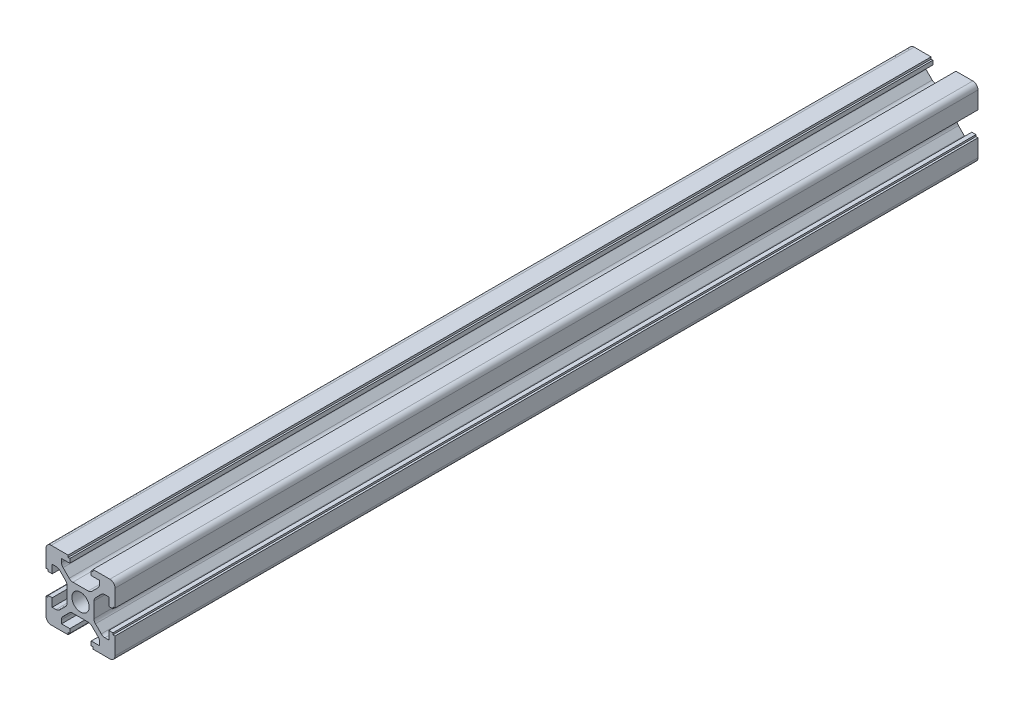
SolidWorks part; units mm, degrees
ref_plane "Front Plane" through (0, 0, 0) normal (0, 0, 1) x (1, 0, 0)
ref_plane "Top Plane" through (0, 0, 0) normal (0, 1, 0) x (1, 0, 0)
ref_plane "Right Plane" through (0, 0, 0) normal (1, 0, 0) x (0, 0, -1)
sketch "Sketch1" plane through (0, 0, 0) normal (0, 0, 1) x (1, 0, 0)
  line L0 (-3.6, -10) -> (-8.5, -10)
  line L1 (-10, -8.5) -> (-10, -3.5)
  line L2 (0, 0) -> (-10, -10) construction
  line L3 (0, 0) -> (0, 11.6126) construction
  line L4 (0, 0) -> (11.7731, -11.7731) construction
  line L5 (8.5, -10) -> (3.6, -10)
  line L6 (10, -8.5) -> (10, -3.5)
  line L7 (3.6, -10) -> (3.6, -9.4)
  line L8 (3.6, -9.4) -> (3.1, -9.4)
  line L9 (3.1, -9.4) -> (3.1, -8.2)
  line L10 (-3.6, -10) -> (-3.6, -9.4)
  line L11 (-3.6, -9.4) -> (-3.1, -9.4)
  line L12 (-3.1, -9.4) -> (-3.1, -8.2)
  line L13 (3.1, -8.2) -> (5.5, -8.2)
  line L14 (-3.1, -8.2) -> (-5.5, -8.2)
  line L15 (-5.5, -8.2) -> (-5.5, -7.182)
  line L16 (-5.0607, -6.1213) -> (-3.2787, -4.3393)
  line L17 (5.5, -8.2) -> (5.5, -7.182)
  line L18 (5.0607, -6.1213) -> (3.2787, -4.3393)
  line L19 (-2.218, -3.9) -> (2.218, -3.9)
  line L20 (-10, -3.5) -> (-9.4, -3.5)
  line L21 (-9.4, -3.5) -> (-9.4, -3)
  line L22 (-9.4, -3) -> (-8.2, -3)
  line L23 (-8.2, -3) -> (-8.2, -5.4)
  line L24 (-8.2, -5.4) -> (-7.082, -5.4)
  line L25 (-6.0213, -4.9607) -> (-4.3393, -3.2787)
  line L26 (-3.9, -2.218) -> (-3.9, 2.218)
  line L27 (10, -3.5) -> (9.4, -3.5)
  line L28 (9.4, -3.5) -> (9.4, -3)
  line L29 (9.4, -3) -> (8.2, -3)
  line L30 (8.2, -3) -> (8.2, -5.4)
  line L31 (8.2, -5.4) -> (7.082, -5.4)
  line L32 (6.0213, -4.9607) -> (4.3393, -3.2787)
  line L33 (3.9, -2.218) -> (3.9, 2.218)
  line L34 (0, 0) -> (-21.3742, 0) construction
  line L35 (6.0213, 4.9607) -> (4.3393, 3.2787)
  line L36 (8.2, 5.4) -> (7.082, 5.4)
  line L37 (8.2, 3) -> (8.2, 5.4)
  line L38 (9.4, 3) -> (8.2, 3)
  line L39 (9.4, 3.5) -> (9.4, 3)
  line L40 (10, 3.5) -> (9.4, 3.5)
  line L41 (10, 8.5) -> (10, 3.5)
  line L42 (8.5, 10) -> (3.6, 10)
  line L43 (3.6, 10) -> (3.6, 9.4)
  line L44 (3.6, 9.4) -> (3.1, 9.4)
  line L45 (3.1, 9.4) -> (3.1, 8.2)
  line L46 (3.1, 8.2) -> (5.5, 8.2)
  line L47 (5.5, 8.2) -> (5.5, 7.182)
  line L48 (5.0607, 6.1213) -> (3.2787, 4.3393)
  line L49 (-2.218, 3.9) -> (2.218, 3.9)
  line L50 (-5.0607, 6.1213) -> (-3.2787, 4.3393)
  line L51 (-5.5, 8.2) -> (-5.5, 7.182)
  line L52 (-3.1, 8.2) -> (-5.5, 8.2)
  line L53 (-3.6, 9.4) -> (-3.1, 9.4)
  line L54 (-3.1, 9.4) -> (-3.1, 8.2)
  line L55 (-3.6, 10) -> (-3.6, 9.4)
  line L56 (-3.6, 10) -> (-8.5, 10)
  line L57 (-10, 8.5) -> (-10, 3.5)
  line L58 (-10, 3.5) -> (-9.4, 3.5)
  line L59 (-9.4, 3.5) -> (-9.4, 3)
  line L60 (-9.4, 3) -> (-8.2, 3)
  line L61 (-8.2, 3) -> (-8.2, 5.4)
  line L62 (-8.2, 5.4) -> (-7.082, 5.4)
  line L63 (-6.0213, 4.9607) -> (-4.3393, 3.2787)
  circle A0 centre (0, 0) radius 2.5
  arc A1 (-10, -8.5) -> (-8.5, -10) centre (-8.5, -8.5) ccw
  arc A2 (10, -8.5) -> (8.5, -10) centre (8.5, -8.5) cw
  arc A3 (10, 8.5) -> (8.5, 10) centre (8.5, 8.5) ccw
  arc A4 (-10, 8.5) -> (-8.5, 10) centre (-8.5, 8.5) cw
  arc A5 (-7.082, -5.4) -> (-6.0213, -4.9607) centre (-7.082, -3.9) ccw
  arc A6 (-7.082, 5.4) -> (-6.0213, 4.9607) centre (-7.082, 3.9) cw
  arc A7 (-5.0607, 6.1213) -> (-5.5, 7.182) centre (-4, 7.182) cw
  arc A8 (5.5, 7.182) -> (5.0607, 6.1213) centre (4, 7.182) cw
  arc A9 (6.0213, 4.9607) -> (7.082, 5.4) centre (7.082, 3.9) cw
  arc A10 (7.082, -5.4) -> (6.0213, -4.9607) centre (7.082, -3.9) cw
  arc A11 (-5.5, -7.182) -> (-5.0607, -6.1213) centre (-4, -7.182) cw
  arc A12 (5.5, -7.182) -> (5.0607, -6.1213) centre (4, -7.182) ccw
  arc A13 (-4.3393, 3.2787) -> (-3.9, 2.218) centre (-5.4, 2.218) cw
  arc A14 (-4.3393, -3.2787) -> (-3.9, -2.218) centre (-5.4, -2.218) ccw
  arc A15 (-3.2787, -4.3393) -> (-2.218, -3.9) centre (-2.218, -5.4) cw
  arc A16 (3.2787, -4.3393) -> (2.218, -3.9) centre (2.218, -5.4) ccw
  arc A17 (4.3393, -3.2787) -> (3.9, -2.218) centre (5.4, -2.218) cw
  arc A18 (4.3393, 3.2787) -> (3.9, 2.218) centre (5.4, 2.218) ccw
  arc A19 (3.2787, 4.3393) -> (2.218, 3.9) centre (2.218, 5.4) cw
  arc A20 (-2.218, 3.9) -> (-3.2787, 4.3393) centre (-2.218, 5.4) cw
  point P16 (10, -10)
  point P17 (4.1697, -5.2303)
  point P45 (3.9, 0)
  point P79 (-3.9, 0)
  point P81 (-6.4607, -5.4)
  point P84 (-6.4607, 5.4)
  point P87 (-5.5, 6.5607)
  point P90 (5.5, 6.5607)
  point P93 (6.4607, 5.4)
  point P96 (6.4607, -5.4)
  point P99 (-5.5, -6.5607)
  point P102 (5.5, -6.5607)
  point P105 (-3.9, 2.8393)
  point P108 (-3.9, -2.8393)
  point P111 (-2.8393, -3.9)
  point P114 (2.8393, -3.9)
  point P117 (3.9, -2.8393)
  point P120 (3.9, 2.8393)
  point P123 (2.8393, 3.9)
  point P126 (-2.8393, 3.9)
  dimension "D1" = 5
  dimension "D5" = 1.5
  dimension "D33" = 1.5
  dimension "D2" = 135
  dimension "D3" = 90
  dimension "D4" = 20
  dimension "D6" = 3.6
  dimension "D7" = 3.6
  dimension "D8" = 0.6
  dimension "D9" = 0.6
  dimension "D10" = 6.2
  dimension "D11" = 3.1
  dimension "D12" = 1.2
  dimension "D13" = 1.2
  dimension "D14" = 11
  dimension "D15" = 5.5
  dimension "D16" = 0.75
  dimension "D17" = 0.75
  dimension "D18" = 6.1
  dimension "D19" = 5
  dimension "D20" = 5
  dimension "D21" = 0.6
  dimension "D22" = 0.5
  dimension "D23" = 1.2
  dimension "D24" = 2.4
  dimension "D25" = 6.1
  dimension "D26" = 1.5
  dimension "D27" = 0.6
  dimension "D28" = 0.5
  dimension "D29" = 1.2
  dimension "D30" = 1.5
  dimension "D31" = 2.4
  dimension "D32" = 6.1
extrude "Boss-Extrude1" add sketch "Sketch1" along normal blind 250
